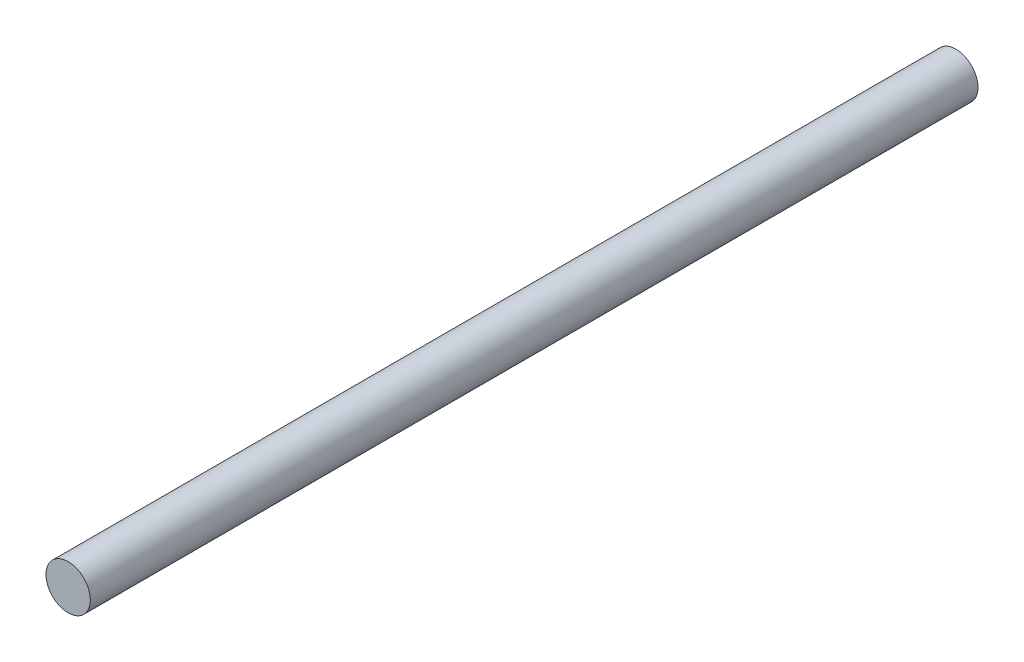
SolidWorks part; units mm, degrees
material "Plain Carbon Steel"
ref_plane "Front Plane" through (0, 0, 0) normal (0, 0, 1) x (1, 0, 0)
ref_plane "Top Plane" through (0, 0, 0) normal (0, 1, 0) x (1, 0, 0)
ref_plane "Right Plane" through (0, 0, 0) normal (1, 0, 0) x (0, 0, -1)
sketch "Sketch1" plane through (0, 0, 0) normal (0, 0, 1) x (1, 0, 0)
  circle A0 centre (0, 0) radius 10
  dimension "Diameter" = 20
extrude "Shaft Extrude" add sketch "Sketch1" along normal blind 400 contours A0
equation "\"Diameter@Sketch1\"=\"ShaftDiameter\""
equation "\"ExtrusionStandard\"= 20mm'Size of extrusion used for framing"
equation "\"BaseExtrusionFrameWidth\"= 60mm"
equation "\"BaseExtrusionFrameHeight\"= 20mm"
equation "\"PlateThickness\"= 15mm"
equation "\"RailHeight\"=13"
equation "\"WallThickness\"= 3mm"
equation "\"ShaftDiameter\"= 20mm"
equation "\"ShaftClearance\"= 1mm"
equation "\"PlainBearingBoltCircleDiameter\"= ( \"WallThickness\" + \"M3_ClearanceDiameter\" / 2 ) * 2 + \"PlainBearingOD\""
equation "\"PlainBearingBoltcount\"=5"
equation "\"ThrustBearingOD\"= 35mm"
equation "\"ThrustBearingID\"= 20mm"
equation "\"ThrustBearingThickness\"= 10mm"
equation "\"RearCollarOD\"= 32mm"
equation "\"RearCollarID\"= 20mm"
equation "\"RearCollarThickness\"= 14mm"
equation "\"LeadScrewDiameter\"= 6.35mm"
equation "\"LeadScrewHeight\"= 10mm'Height of Lead screw from bottom of gantry extrusion"
equation "\"LeadScrewNut_FlangeOD\"= 25mm'OD of the lead screw nut flange"
equation "\"LeadScrewNut_BoltCircleDiameter\"= 19mm"
equation "\"LeadScrewNut_BoltCount\"= 6"
equation "\"ShaftOffset_BaseThickness\"= 6mm + \"WallThickness\""
equation "\"PillowHeight\"= \"ShaftOffset_BaseThickness\" + \"ExtrusionStandard\""
equation "\"X_BeltPitch\"= 2mm"
equation "\"X_Drive_Teeth\"= 20"
equation "\"X_Shaft_Teeth\"= 60"
equation "\"X_Drive_PD\"= ( \"X_Drive_Teeth\" * \"X_BeltPitch\" ) / PI"
equation "\"X_Shaft_PD\"= ( \"X_Shaft_Teeth\" * \"X_BeltPitch\" ) / PI"
equation "\"X_CenterDistance\"= 55mm"
equation "\"GantryLength\"= 150mm'Length of the gantry extrusion/plate"
equation "\"X_MotorPlateThickness\"= 15mm"
equation "\"X_MotorPlateLength\"= \"X_MotorPlateThickness\" + \"ExtrusionStandard\" * 2"
equation "\"X_BeltWidth\"= 10mm"
equation "\"X_PillowLength\"= ( \"WallThickness\" * 4 ) + \"RearCollarThickness\" + ( \"ThrustBearingThickness\" * 2 ) + \"ShaftRotaryBearingThickness\""
equation "\"ShaftRotaryBearingThickness\"= 9mm"
equation "\"ShaftRotaryBearingOD\"= 37mm"
equation "\"ShaftLength\"= 400mm'Length of the main shaft.\\"
equation "\"D1@Shaft Extrude\"=\"ShaftLength\""
